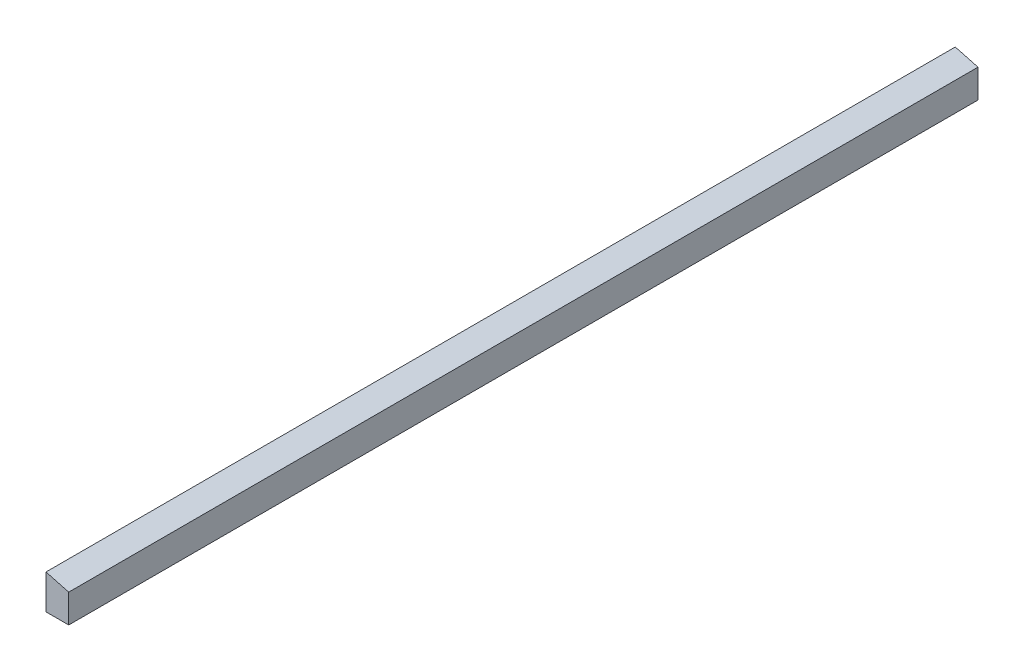
SolidWorks part; units mm, degrees
material "Pine"
ref_plane "Front Plane" through (0, 0, 0) normal (0, 0, 1) x (1, 0, 0)
ref_plane "Top Plane" through (0, 0, 0) normal (0, 1, 0) x (1, 0, 0)
ref_plane "Right Plane" through (0, 0, 0) normal (1, 0, 0) x (0, 0, -1)
sketch "Sketch1" plane through (0, 0, 0) normal (0, 0, 1) x (1, 0, 0)
  line L0 (-22.7606, 27.4333) -> (15.3394, 17.2244)
  line L2 (-22.7606, 27.4333) -> (-22.7606, -30.5105)
  line L3 (-22.7606, -30.5105) -> (15.3394, -30.5105)
  line L4 (15.3394, 17.2244) -> (15.3394, -30.5105)
  line L5 (-22.7606, -30.5105) -> (-22.7606, 45.6895) construction
  line L6 (-22.7606, 27.4333) -> (-14.4544, 45.6895) construction
  dimension "D1" = 57.9437
  dimension "D2" = 38.1
  dimension "D3" = 75
  dimension "D4" = 76.2
extrude "Boss-Extrude1" add sketch "Sketch1" along normal blind 1524
